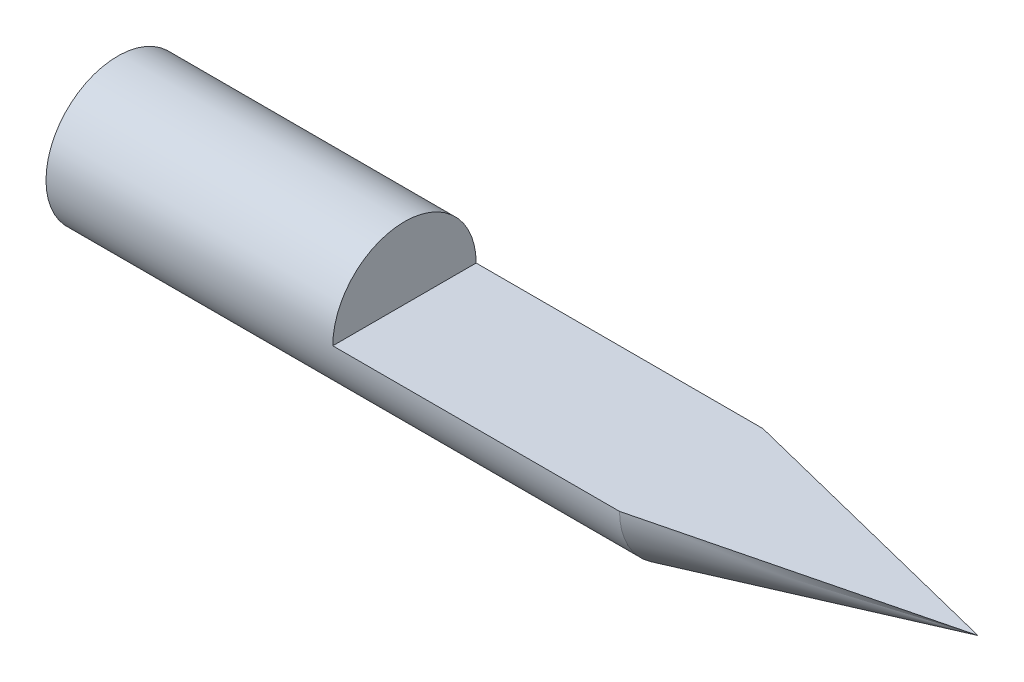
SolidWorks part; units mm, degrees
ref_plane "Front Plane" through (0, 0, 0) normal (0, 0, 1) x (1, 0, 0)
ref_plane "Top Plane" through (0, 0, 0) normal (0, 1, 0) x (1, 0, 0)
ref_plane "Right Plane" through (0, 0, 0) normal (1, 0, 0) x (0, 0, -1)
sketch "Sketch1" plane through (0, 0, 0) normal (0, 0, 1) x (1, 0, 0)
  line L0 (15, -1.25) -> (5, 1.25)
  line L1 (-15, 1.25) -> (5, 1.25)
  line L2 (-15, 1.25) -> (-15, -1.25)
  line L3 (-15, -1.25) -> (15, -1.25)
  line L4 (15, 1.25) -> (15, -1.25) construction
  line L5 (-15, 1.25) -> (15, -1.25) construction
  line L6 (-15, -1.25) -> (15, 1.25) construction
  line L7 (5, 1.25) -> (15, 1.25) construction
  point P0 (0, 0)
  dimension "D1" = 30
  dimension "D2" = 2.5
  dimension "D3" = 20
revolve "Revolve2" add sketch "Sketch1" angle 360 about L3
ref_plane "Plane1" through (5, 0, 0) normal (1, 0, 0) x (0, 0, -1)
sketch "Sketch2" plane through (5, 0, 0) normal (1, 0, 0) x (0, 0, -1)
  line L0 (-2.5, -1.25) -> (2.5, -1.25)
  arc A0 (2.5, -1.25) -> (-2.5, -1.25) centre (0, -1.25) ccw
  arc A1 (-2.5, -1.25) -> (2.5, -1.25) centre (0, -1.25) ccw construction
extrude "Cut-Extrude1" cut sketch "Sketch2" against normal mid plane 20
